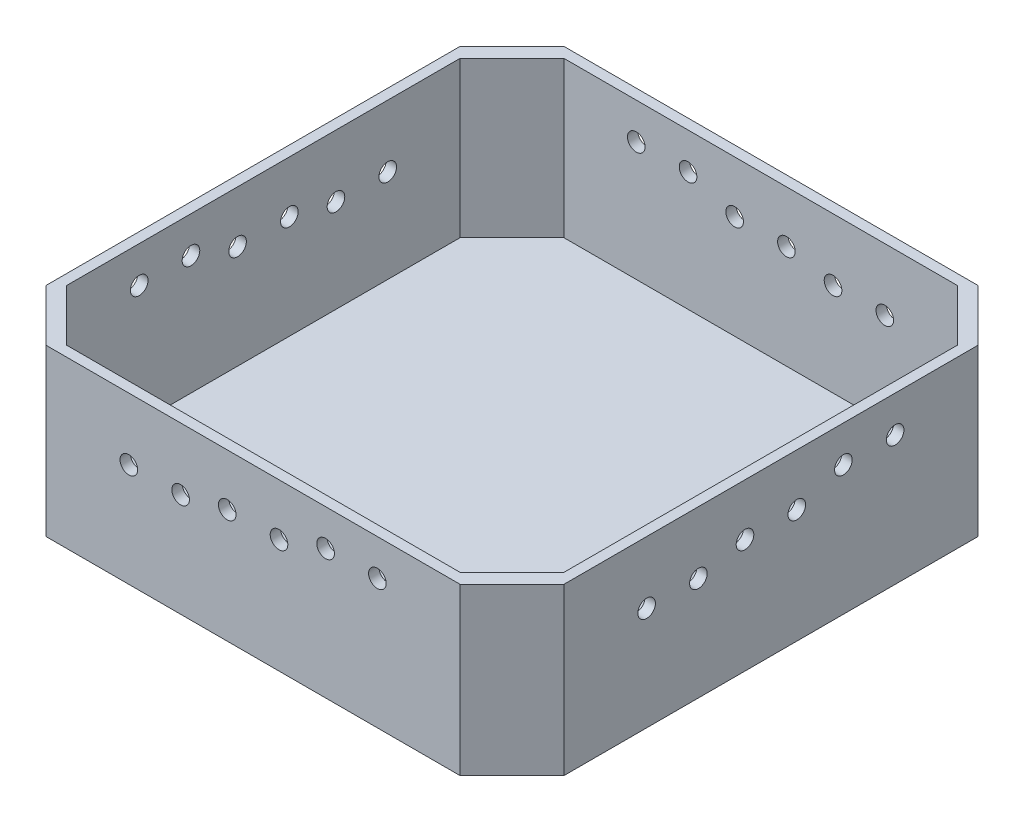
SolidWorks part; units mm, degrees
material "PLA Black"
ref_plane "Front" through (0, 0, 0) normal (0, 0, 1) x (1, 0, 0)
ref_plane "Top" through (0, 0, 0) normal (0, 1, 0) x (1, 0, 0)
ref_plane "Right" through (0, 0, 0) normal (1, 0, 0) x (0, 0, -1)
sketch "Sketch1" plane through (0, 0, 0) normal (0, 1, 0) x (1, 0, 0)
  line L0 (0, -50) -> (0, 50) construction
  line L1 (-50, 50) -> (50, 50)
  line L2 (-50, 50) -> (-50, -50)
  line L3 (-50, -50) -> (50, -50)
  line L4 (50, 50) -> (50, -50)
  dimension "D1" = 100
extrude "Boss-Extrude1" add sketch "Sketch1" along normal blind 2
sketch "Sketch2" plane through (0, 2, 0) normal (0, 1, 0) x (1, 0, 0)
  line L0 (-48, 48) -> (-48, -48)
  line L1 (-48, -48) -> (48, -48)
  line L2 (48, -48) -> (48, 48)
  line L3 (48, 48) -> (-48, 48)
  line L4 (-50, 50) -> (-50, -50)
  line L5 (-50, -50) -> (50, -50)
  line L6 (50, -50) -> (50, 50)
  line L7 (50, 50) -> (-50, 50)
  line L8 (-50, 50) -> (-50, -50)
  line L9 (-50, -50) -> (50, -50)
  line L10 (50, -50) -> (50, 50)
  line L11 (50, 50) -> (-50, 50)
  dimension "D1" = 0
  dimension "D2" = 2
extrude "Boss-Extrude2" add sketch "Sketch2" along normal blind 30
chamfer "Chamfer1" distance 10 angle 45 8 edges at (48, 17, 48) (-48, 17, 48) (-50, 16, 50) (-50, 16, -50) (48, 17, -48) (-48, 17, -48) (50, 16, -50) (50, 16, 50)
hole_wizard "M3 Clearance Hole1" positions "Sketch4" profile "Sketch3" hole size "M3" standard "DIN"
sketch "Sketch4" plane through (0, 0, -48) normal (0, 0, 1) x (1, 0, 0)
  line L0 (0, 0) -> (0, 32) construction
  line L2 (19, 27.2112) -> (19, 6.0838) construction
  line L4 (-19, 27.2112) -> (-19, 10.8349) construction
  line L6 (14, 20) -> (24, 20) construction
  line L8 (-5, 22) -> (5, 22) construction
  line L10 (-24, 25) -> (-14, 25) construction
  line L12 (38, 32) -> (-38, 32) construction
  point P0 (-24, 25)
  point P2 (-14, 25)
  point P4 (-5, 22)
  point P6 (5, 22)
  point P8 (14, 20)
  point P10 (24, 20)
  dimension "D1" = 10
  dimension "D2" = 7
  dimension "D3" = 10
  dimension "D4" = 12
sketch "Sketch3" plane through (-24, 25, -48) normal (1, 0, 0) x (0, -1, 0)
  line L0 (0, 0) -> (0, 6.0215)
  line L1 (0, 6.0215) -> (1.7, 5)
  line L2 (1.7, 5) -> (1.7, 0)
  line L5 (1.7, 0) -> (0, 0)
  line L10 (0, 6.0215) -> (-1.7, 5) construction
  line L11 (0, -6.35) -> (0, 107.95) construction
  dimension "Hole Dia." = 3.4
  dimension "Hole Depth" = 5
  dimension "Drill Angle" = 118
ref_axis "Axis1" through (0, 50, 0) along (0, -1, 0)
pattern_circular "CirPattern1" count 4 over 360 about axis through (0, 50, 0) along (0, -1, 0) of "M3 Clearance Hole1"
